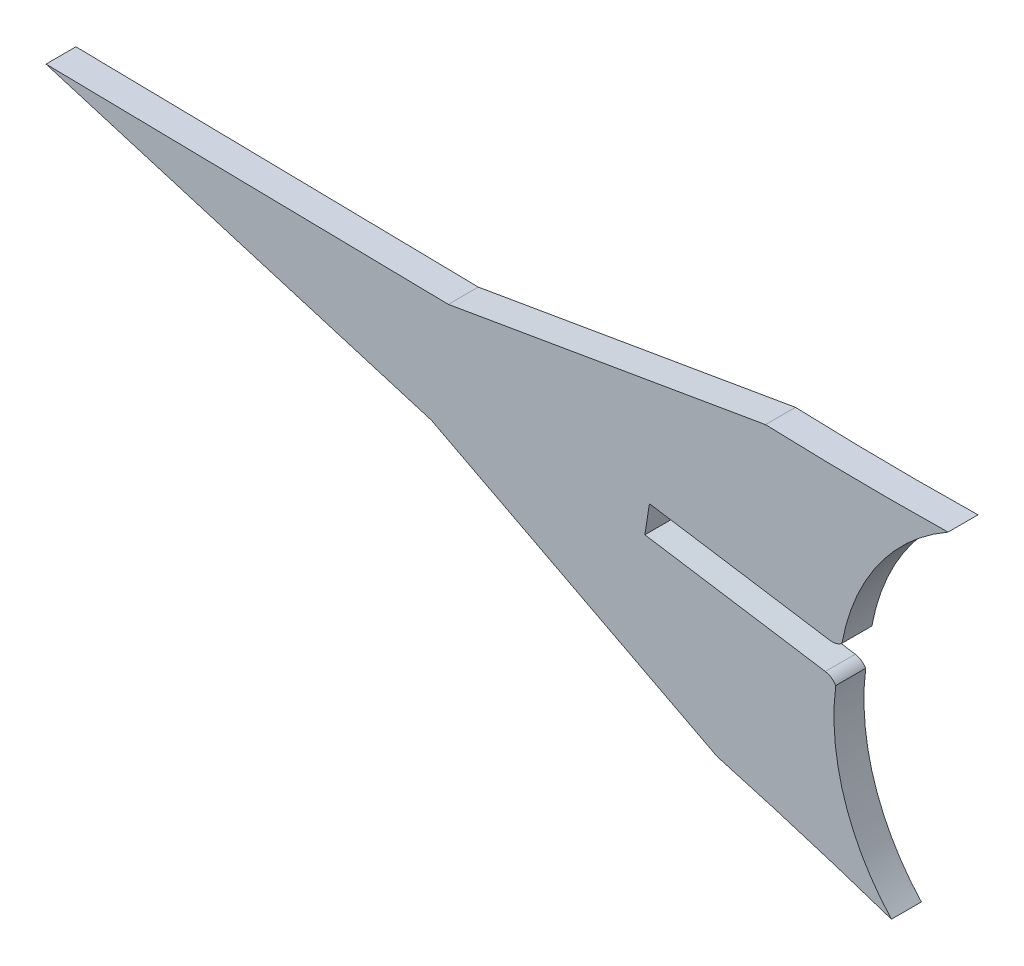
SolidWorks part; units mm, degrees
ref_plane "Front Plane" through (0, 0, 0) normal (0, 0, 1) x (1, 0, 0)
ref_plane "Top Plane" through (0, 0, 0) normal (0, 1, 0) x (1, 0, 0)
ref_plane "Right Plane" through (0, 0, 0) normal (1, 0, 0) x (0, 0, -1)
sketch "Sketch1" plane through (0, 0, 0) normal (0, 0, 1) x (1, 0, 0)
  line L0 (243.1253, 227.2279) -> (230.0247, 229.2685) construction
  line L1 (243.0094, 226.4836) -> (252.1965, 225.0514)
  line L2 (212.5212, 231.9949) -> (232.1415, 226.1013)
  line L3 (246.6821, 218.5493) -> (232.1415, 226.1013)
  line L155 (249.1532, 234.4136) -> (233.0045, 231.6418)
  line L157 (212.5212, 231.9949) -> (233.0045, 231.6418)
  line L159 (243.0094, 226.4836) -> (243.2413, 227.9722)
  line L160 (243.2413, 227.9722) -> (252.4287, 226.5424)
  arc A0 (252.1965, 225.0514) -> (252.7282, 224.6976) centre (252.0791, 224.2985) cw
  arc A1 (258.4453, 234.3208) -> (249.1532, 234.4136) centre (255.4644, 401.0844) cw
  arc A2 (252.7282, 224.6976) -> (255.5622, 215.8115) centre (263.66, 223.2891) ccw
  arc A3 (255.5622, 215.8115) -> (246.6821, 218.5493) centre (202.0015, 57.855) ccw
  arc A4 (253.0428, 226.7176) -> (258.4453, 234.3208) centre (263.8852, 224.7345) cw
  arc A573 (252.4287, 226.5424) -> (253.0428, 226.7176) centre (252.5459, 227.2953) ccw
extrude "Boss-Extrude1" add sketch "Sketch1" along normal blind 1.524
